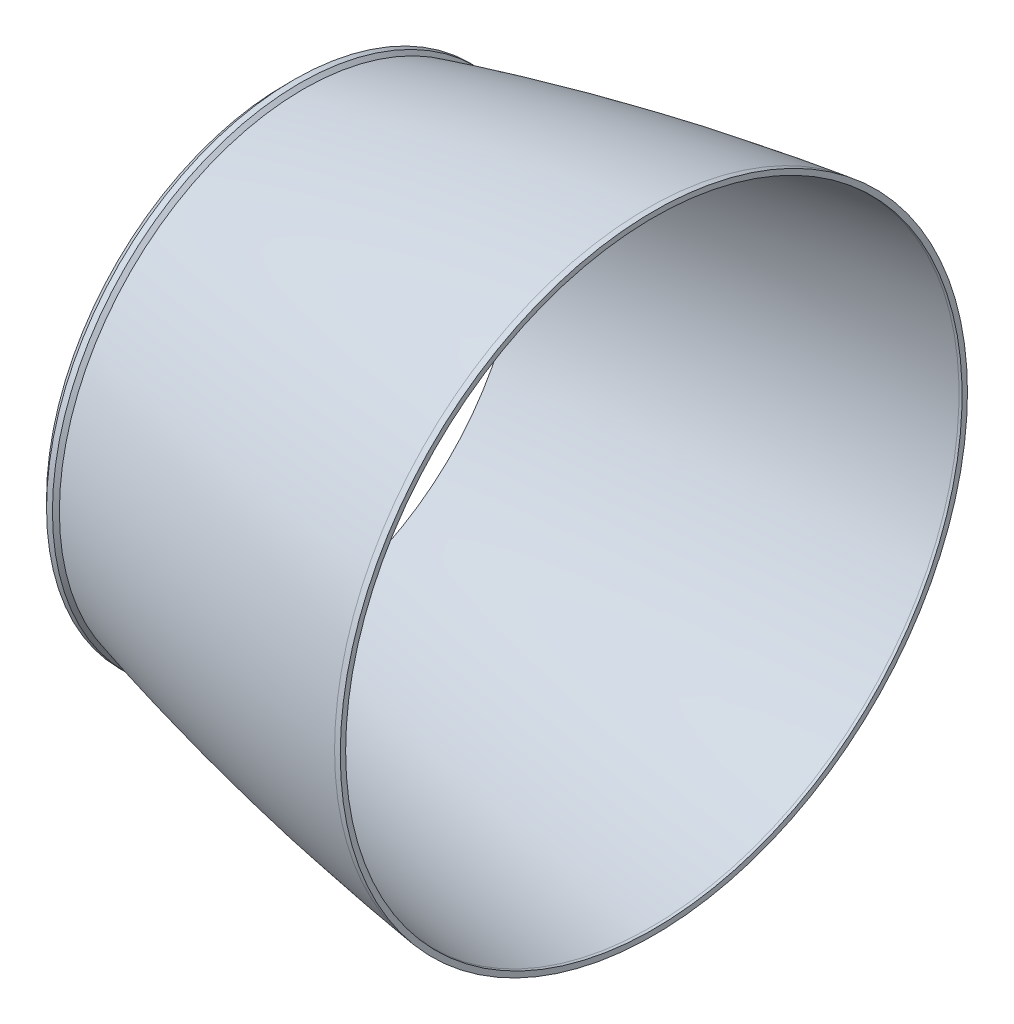
SolidWorks part; units mm, degrees
material "Бронза с оловом"
ref_plane "Спереди" through (0, 0, 0) normal (0, 0, 1) x (1, 0, 0)
ref_plane "Сверху" through (0, 0, 0) normal (0, 1, 0) x (1, 0, 0)
ref_plane "Справа" through (0, 0, 0) normal (1, 0, 0) x (0, 0, -1)
sketch "Эскиз3" plane through (0, 0, 0) normal (0, 1, 0) x (1, 0, 0)
  line L0 (689.4882, 261.2232) -> (691.794, 261.527)
  line L1 (686.2321, 265.354) -> (691.794, 266.0901)
  line L2 (0, 0) -> (979.6178, 0) construction
  line L3 (691.794, 0) -> (691.794, 276.5373) construction
  line L5 (691.794, 266.0901) -> (691.794, 261.527)
  line L6 (379.354, 202.8622) -> (379.354, 198.0007)
  line L7 (379.354, 202.8622) -> (386.354, 209.8622)
  line L8 (386.354, 209.8622) -> (391.354, 209.8622)
  line L9 (391.354, 209.8622) -> (394.354, 206.9716)
  line L10 (394.354, 206.9716) -> (394.2081, 204.348)
  line L11 (394.2081, 204.348) -> (386.9364, 202.3783)
  line L12 (386.9364, 202.3783) -> (379.354, 202.8622)
  line L13 (686.794, 265.4284) -> (683.4154, 268.8069)
  line L14 (683.4154, 268.8069) -> (678.4233, 268.527)
  line L15 (678.4233, 268.527) -> (670.26, 263.1831)
  line L25 (379.354, 198.0007) -> (379.354, 202.8622) construction
  spline S2 degree 3 poles (379.354, 198.0007) (404.4328, 204.994) (455.1844, 218.1906) (532.2462, 235.3494) (597.4015, 247.4516) (649.8879, 255.7728) (676.2852, 259.4843) (689.4882, 261.2232) knots 0.559678 0.559678 0.559678 0.559678 0.667303 0.776468 0.885632 0.940214 0.994797 0.994797 0.994797 0.994797
  spline S4 degree 3 poles (379.354, 202.8622) (403.6062, 209.5975) (453.4481, 222.5338) (529.4998, 239.4865) (594.446, 251.5763) (646.762, 259.8976) (673.0724, 263.6125) (686.2321, 265.354) knots 0.56291 0.56291 0.56291 0.56291 0.66682 0.775501 0.884182 0.938522 0.992863 0.992863 0.992863 0.992863
  dimension "D1" = 45
  dimension "D2" = 312.44
  dimension "D3" = 15
  dimension "D4" = 5
  dimension "D5" = 7
  dimension "D6" = 5
  dimension "D7" = 45
  dimension "D8" = 5
  dimension "D10" = 150
  dimension "D11" = 7
revolve "Повернуть2" add sketch "Эскиз3" angle 360 about L2
equation "\"dкр\"= 65.43мм"
equation "\"rкр\"= 14.83мм"
equation "\"da\"= 515.41мм"
equation "\"Bm\"= 34градусов"
equation "\"Ba\"= 9градусов"
equation "\"Lсверх\"= 693.56мм"
equation "\"Pascal\"= 200мм"
equation "\"dк\"= 173.0мм"
equation "\"Lк\"= 243.6мм"
equation "\"h\"= 4.15мм"
equation "\"lвх\"= 15.07мм"
equation "\"R1\"= 65.43мм"
equation "\"Rскр\"= 4.95мм"
equation "\"Lц\"= 134.47мм"
equation "\"anchura\"= 2"
equation "\"a\"= 4мм'comienza le рёбр"
equation "\"b\"=2"
equation "\"hробре\"= 2мм"
